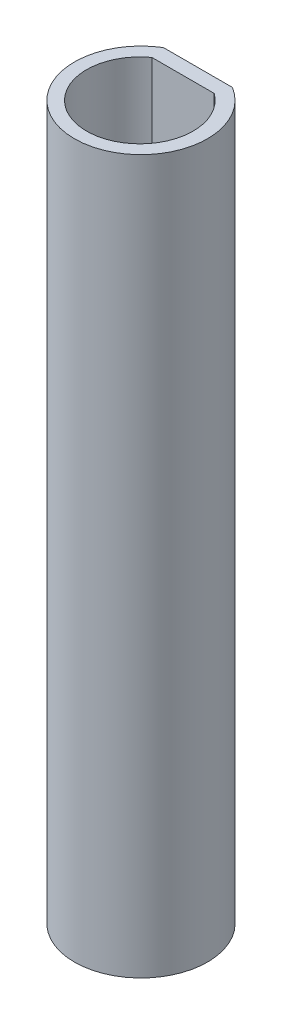
SolidWorks part; units mm, degrees
ref_plane "Front Plane" through (0, 0, 0) normal (0, 0, 1) x (1, 0, 0)
ref_plane "Top Plane" through (0, 0, 0) normal (0, 1, 0) x (1, 0, 0)
ref_plane "Right Plane" through (0, 0, 0) normal (1, 0, 0) x (0, 0, -1)
sketch "Sketch1" plane through (0, 0, 0) normal (0, 1, 0) x (1, 0, 0)
  line L0 (-0.725, 1.1977) -> (0.725, 1.1977)
  arc A0 (-0.725, 1.1977) -> (0.725, 1.1977) centre (0, 0) ccw
  dimension "D1" = 1.4
  dimension "D2" = 1.45
extrude "Boss-Extrude1" add sketch "Sketch1" along normal blind 15
sketch "Sketch2" plane through (0, 0, 0) normal (0, -1, 0) x (1, 0, 0)
  line L0 (0.644, -0.8969) -> (-0.6665, -0.8969)
  arc A0 (0.644, -0.8969) -> (-0.6665, -0.8969) centre (-0.0112, 0.0125) ccw
extrude "Cut-Extrude1" cut sketch "Sketch2" against normal through all
